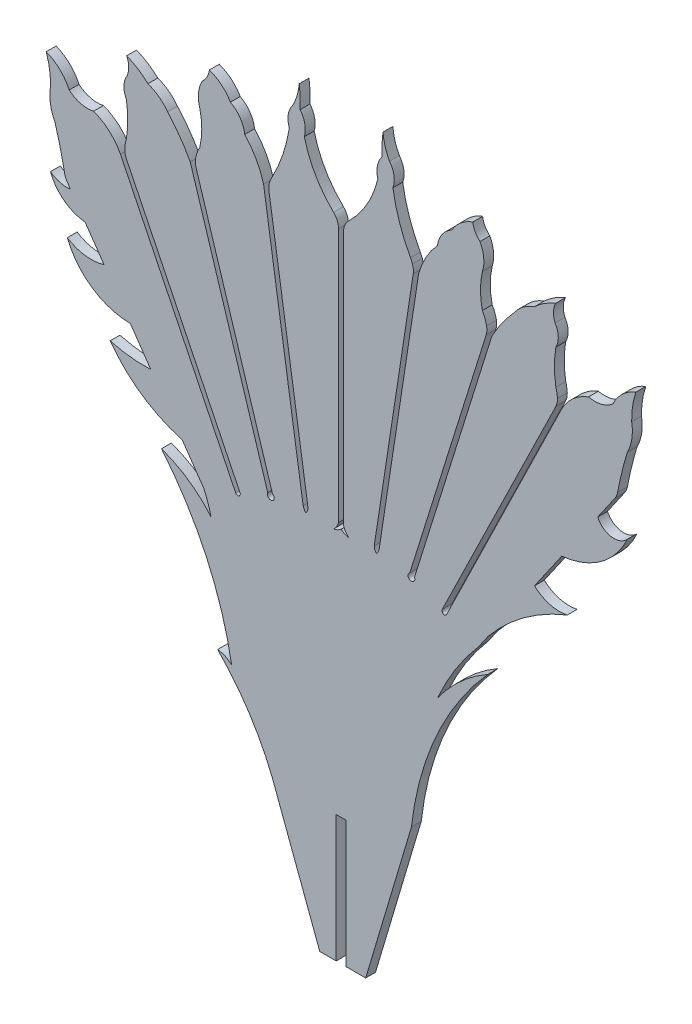
SolidWorks part; units mm, degrees
ref_plane "Front Plane" through (0, 0, 0) normal (0, 0, 1) x (1, 0, 0)
ref_plane "Top Plane" through (0, 0, 0) normal (0, 1, 0) x (1, 0, 0)
ref_plane "Right Plane" through (0, 0, 0) normal (1, 0, 0) x (0, 0, -1)
sketch "Sketch1" plane through (0, 0, 0) normal (0, 0, 1) x (1, 0, 0)
  line L0 (11.364, 5.9481) -> (23.2812, 44.0618)
  line L1 (5.8842, 6.9405) -> (12.0096, 47.0057)
  line L2 (0.3802, 7.433) -> (0.3752, 46.8125)
  line L3 (-0.0008, 7.4329) -> (-0.006, 48.0787) construction
  line L4 (39.7473, 28.2348) -> (42.4168, 32.0864)
  line L5 (29.9549, 14.1063) -> (34.1754, 20.1956)
  line L6 (-39.6525, 28.0842) -> (-36.7126, 23.8436)
  line L7 (-3.3071, -51.5841) -> (-0.7639, -51.5839)
  line L8 (0.7601, -51.5838) -> (3.8062, -51.5836)
  line L9 (-10.6663, -31.9331) -> (-3.3071, -51.5841)
  line L10 (16.3385, 3.445) -> (34.1754, 39.9499)
  line L11 (15.6539, 3.7796) -> (33.2536, 39.7899)
  line L12 (10.6367, 6.1755) -> (22.47, 44.021)
  line L13 (-42.4228, 32.0801) -> (-41.9238, 31.3603)
  line L14 (21.2769, 1.5857) -> (22.7474, 3.7073)
  line L15 (3.8062, -51.5836) -> (10.894, -27.7824)
  line L16 (5.1309, 7.0556) -> (11.1735, 46.5786)
  line L17 (-0.3818, 7.4329) -> (-0.3868, 46.8144)
  line L18 (-32.6597, 17.9978) -> (-29.4821, 13.4144)
  line L19 (-5.1324, 7.0543) -> (-11.1823, 46.5576)
  line L20 (-0.006, -53.6384) -> (-0.006, -31.9335) construction
  line L21 (0.7601, -51.5838) -> (0.7587, -31.9322)
  line L22 (-0.7639, -51.5839) -> (-0.7653, -31.9323)
  line L23 (-24.6395, 6.4293) -> (-21.2793, 1.5825)
  line L24 (0.7587, -31.9322) -> (-0.7653, -31.9323)
  line L25 (-10.638, 6.1728) -> (-22.4757, 43.9984)
  line L28 (-15.6546, 3.7756) -> (-33.2559, 39.7658)
  line L29 (-16.3391, 3.4408) -> (-34.1926, 39.9536)
  line L31 (-5.8857, 6.939) -> (-12.0115, 47.0061)
  line L32 (-11.3652, 5.9453) -> (-23.3699, 44.3244)
  arc A0 (10.894, -27.7824) -> (22.7474, -1.3651) centre (57.8292, -32.9742) cw
  arc A1 (22.7474, -1.3651) -> (14.9246, -8.4598) centre (35.0474, -22.7873) ccw
  arc A2 (14.9246, -8.4598) -> (21.2769, 1.5857) centre (51.5441, -24.5847) cw
  arc A3 (42.8251, 33.0617) -> (44.3326, 39.2037) centre (100.4541, 22.1724) cw
  arc A4 (44.3326, 39.2037) -> (45.0118, 43.6422) centre (38.1266, 42.4246) ccw
  arc A5 (-42.8311, 33.0553) -> (-42.4228, 32.0801) centre (-40.3354, 33.5273) ccw
  arc A6 (42.4168, 32.0864) -> (42.8251, 33.0617) centre (40.3292, 33.5333) ccw
  arc A7 (-16.9494, -20.0081) -> (-19.1335, -18.9781) centre (-19.3922, -22.3573) ccw
  arc A8 (-5.6955, 56.5343) -> (-1.1658, 48.6445) centre (10.1073, 60.3618) ccw
  arc A9 (-6.3378, 59.8346) -> (-5.6955, 56.5343) centre (-9.2555, 57.5541) cw
  arc A10 (-6.4948, 63.2426) -> (-6.3378, 59.8346) centre (-27.5257, 60.5664) cw
  arc A11 (-7.5047, 59.8346) -> (-6.4948, 63.2426) centre (-14.9546, 63.896) ccw
  arc A12 (-8.0255, 56.5343) -> (-7.5047, 59.8346) centre (-4.8207, 57.7198) cw
  arc A13 (-10.6689, 48.6671) -> (-8.0255, 56.5343) centre (-32.5915, 60.4108) ccw
  arc A14 (-14.9254, 52.2304) -> (-12.0115, 47.0061) centre (-24.1725, 43.648) cw
  arc A15 (1.1559, 48.6449) -> (0.3752, 46.8125) centre (2.9152, 46.8129) ccw
  arc A16 (11.051, 47.827) -> (10.7457, 48.5219) centre (5.6939, 45.8878) ccw
  arc A17 (11.051, 47.827) -> (11.1735, 46.5786) centre (8.6626, 46.9625) cw
  arc A18 (22.5382, 45.2682) -> (21.8892, 47.0061) centre (16.9495, 44.1712) ccw
  arc A19 (23.4842, 44.5357) -> (23.2812, 44.0618) centre (25.7054, 43.3038) ccw
  arc A20 (33.5094, 41.0122) -> (33.2707, 42.4205) centre (27.8196, 40.7724) ccw
  arc A21 (33.5094, 41.0122) -> (33.2536, 39.7899) centre (30.9716, 40.9052) cw
  arc A22 (33.2707, 42.4205) -> (33.2707, 47.7877) centre (48.3076, 45.1041) cw
  arc A23 (45.0118, 43.6422) -> (45.6713, 47.9529) centre (57.1581, 43.9899) cw
  arc A24 (45.6713, 47.9529) -> (42.1137, 44.5936) centre (48.0445, 41.8761) ccw
  arc A25 (42.1137, 44.5936) -> (38.3293, 43.6417) centre (39.2973, 47.7919) cw
  arc A26 (38.3293, 43.6417) -> (34.1754, 39.9499) centre (41.0901, 36.3525) ccw
  arc A27 (33.2707, 47.7877) -> (33.1585, 50.9543) centre (30.4877, 49.2743) ccw
  arc A28 (33.1585, 50.9543) -> (33.2176, 53.6358) centre (36.1189, 52.2304) cw
  arc A29 (33.2176, 53.6358) -> (29.9243, 51.5238) centre (37.039, 44.0534) ccw
  arc A30 (29.9243, 51.5238) -> (26.8747, 49.2743) centre (31.9678, 45.5616) ccw
  arc A31 (26.8747, 49.2743) -> (23.4842, 44.5357) centre (45.7445, 32.1903) ccw
  arc A32 (21.8892, 47.0061) -> (21.8892, 52.2304) centre (32.9235, 49.6182) cw
  arc A33 (21.8892, 52.2304) -> (21.5156, 56.0773) centre (17.1432, 53.7111) ccw
  arc A34 (21.5156, 56.0773) -> (20.3991, 58.1405) centre (23.6326, 58.5567) cw
  arc A35 (20.3991, 58.1405) -> (17.1432, 55.4334) centre (22.4819, 52.3239) ccw
  arc A36 (17.1432, 55.4334) -> (14.9237, 52.2304) centre (19.1335, 51.6838) ccw
  arc A37 (14.9237, 52.2304) -> (12.0099, 47.0061) centre (24.1709, 43.648) ccw
  arc A38 (10.7457, 48.5219) -> (8.0239, 56.5343) centre (32.5899, 60.4108) cw
  arc A39 (8.0239, 56.5343) -> (7.5031, 59.8346) centre (4.8191, 57.7198) ccw
  arc A40 (7.5031, 59.8346) -> (6.4932, 63.2426) centre (14.953, 63.896) cw
  arc A41 (6.4932, 63.2426) -> (6.3362, 59.8346) centre (27.5241, 60.5664) ccw
  arc A42 (6.3362, 59.8346) -> (5.6939, 56.5343) centre (9.2538, 57.5541) ccw
  arc A43 (5.6939, 56.5343) -> (1.1559, 48.6449) centre (-10.1062, 60.3728) cw
  arc A44 (-17.1448, 55.4334) -> (-14.9254, 52.2304) centre (-19.1352, 51.6838) cw
  arc A45 (-20.4007, 58.1405) -> (-17.1448, 55.4334) centre (-22.4836, 52.3239) cw
  arc A46 (-21.5172, 56.0773) -> (-20.4007, 58.1405) centre (-23.6343, 58.5567) ccw
  arc A47 (-21.8908, 52.2304) -> (-21.5172, 56.0773) centre (-17.1448, 53.7111) cw
  arc A48 (-21.8908, 47.0061) -> (-21.8908, 52.2304) centre (-32.9252, 49.6182) ccw
  arc A49 (-26.8764, 49.2743) -> (-23.3699, 44.3244) centre (-45.7461, 32.1903) cw
  arc A50 (-29.926, 51.5238) -> (-26.8764, 49.2743) centre (-31.9694, 45.5616) cw
  arc A51 (-33.2193, 53.6358) -> (-29.926, 51.5238) centre (-37.0407, 44.0534) cw
  arc A52 (-33.1601, 50.9543) -> (-33.2193, 53.6358) centre (-36.1206, 52.2304) ccw
  arc A53 (-33.2723, 47.7877) -> (-33.1601, 50.9543) centre (-30.4893, 49.2743) cw
  arc A54 (-38.337, 43.636) -> (-34.1926, 39.9536) centre (-41.1035, 36.349) cw
  arc A55 (-42.1215, 44.5873) -> (-38.337, 43.636) centre (-39.3056, 47.786) ccw
  arc A56 (-45.6796, 47.9461) -> (-42.1215, 44.5873) centre (-48.0519, 41.8689) cw
  arc A57 (-45.0195, 43.6355) -> (-45.6796, 47.9461) centre (-57.1658, 43.9813) ccw
  arc A58 (-33.2723, 42.4205) -> (-33.2723, 47.7877) centre (-48.3092, 45.1041) ccw
  arc A59 (-22.5475, 45.2285) -> (-22.4757, 43.9984) centre (-20.0516, 44.757) ccw
  arc A60 (-33.5126, 40.9698) -> (-33.2723, 42.4205) centre (-27.8212, 40.7724) cw
  arc A61 (-11.0658, 47.7903) -> (-11.1823, 46.5576) centre (-8.6716, 46.9421) ccw
  arc A62 (-22.5475, 45.2285) -> (-21.8908, 47.0061) centre (-16.9512, 44.1712) cw
  arc A63 (-1.1658, 48.6445) -> (-0.3868, 46.8144) centre (-2.9268, 46.8141) cw
  arc A64 (-11.0658, 47.7903) -> (-10.6689, 48.6671) centre (-5.6955, 45.8878) cw
  arc A65 (-44.3396, 39.197) -> (-45.0195, 43.6355) centre (-38.1341, 42.4188) cw
  arc A66 (-42.8311, 33.0553) -> (-44.3396, 39.197) centre (-100.4586, 22.1573) ccw
  arc A67 (-10.6663, -31.9331) -> (-19.1335, -18.9781) centre (-47.011, -46.4431) ccw
  arc A68 (12.0096, 47.0057) -> (12.0099, 47.0061) centre (11.6576, 47.2244) ccw
  arc A69 (-16.9494, -20.0081) -> (-27.8212, 3.6114) centre (-66.7129, -28.6019) ccw
  arc A70 (-27.8212, 3.6114) -> (-20.1451, -1.7088) centre (-33.6744, -13.0312) cw
  arc A71 (-20.1451, -1.7088) -> (-21.2793, 1.5825) centre (-34.8286, -4.9272) ccw
  arc A72 (22.47, 44.021) -> (22.5382, 45.2682) centre (20.0458, 44.779) ccw
  arc A73 (-16.3391, 3.4408) -> (-15.6546, 3.7756) centre (-15.9968, 3.6082) ccw
  arc A74 (-33.5126, 40.9698) -> (-33.2559, 39.7658) centre (-30.9741, 40.8817) ccw
  arc A75 (-11.3652, 5.9453) -> (-10.638, 6.1728) centre (-10.8928, 5.7114) ccw
  arc A76 (-5.8857, 6.939) -> (-5.504, 6.1728) centre (-3.714, 7.5427) ccw
  arc A77 (-5.504, 6.1728) -> (-5.1324, 7.0543) centre (-6.3825, 7.0622) ccw
  arc A78 (-0.3818, 7.4329) -> (-1.1658, 6.1728) centre (-2.9676, 8.1678) cw
  arc A79 (-1.1658, 6.1728) -> (-0.0007, 6.7198) centre (-1.5973, 8.6063) ccw
  arc A80 (1.1645, 6.1731) -> (-0.0007, 6.7198) centre (1.5954, 8.6067) cw
  arc A81 (0.3802, 7.433) -> (1.1645, 6.1731) centre (2.9658, 8.1686) ccw
  arc A82 (5.5027, 6.1742) -> (5.1309, 7.0556) centre (6.381, 7.0638) cw
  arc A83 (5.8842, 6.9405) -> (5.5027, 6.1742) centre (3.7123, 7.5436) cw
  arc A84 (11.364, 5.9481) -> (10.6367, 6.1755) centre (10.8916, 5.7142) cw
  arc A85 (16.3385, 3.445) -> (15.6539, 3.7796) centre (15.9962, 3.6123) cw
  arc A86 (22.7474, 3.7073) -> (35.0474, 12.7332) centre (46.2929, -15.4854) cw
  arc A87 (35.0474, 12.7332) -> (29.9549, 14.1063) centre (33.8052, 18.2565) cw
  arc A88 (34.1754, 20.1956) -> (44.3326, 27.5405) centre (32.9222, 32.6244) ccw
  arc A89 (44.3326, 27.5405) -> (39.7473, 28.2348) centre (42.2635, 29.364) cw
  arc A90 (-24.6395, 6.4293) -> (-35.7816, 14.1063) centre (-19.287, 26.1218) cw
  arc A91 (-35.7816, 14.1063) -> (-29.4821, 13.4144) centre (-30.4985, 33.1845) ccw
  arc A92 (-32.6597, 17.9978) -> (-42.4228, 24.6247) centre (-32.6054, 28.583) cw
  arc A93 (-42.4228, 24.6247) -> (-36.7126, 23.8436) centre (-38.7108, 30.4989) ccw
  arc A94 (-39.6525, 28.0842) -> (-45.0195, 32.1903) centre (-39.0624, 34.416) cw
  arc A95 (-45.0195, 32.1903) -> (-41.9238, 31.3603) centre (-42.4359, 35.6387) ccw
  point P8 (0.756, -53.6384)
  point P11 (-0.768, -53.6384)
  point P35 (34.2511, 40.0954)
  point P45 (23.0469, 44.5892)
  point P78 (12.0342, 47.1668)
  point P85 (10.8916, 5.7142)
  point P88 (33.5665, 40.43)
  point P116 (11.281, 47.282)
extrude "Boss-Extrude1" add sketch "Sketch1" along normal blind 1.524
